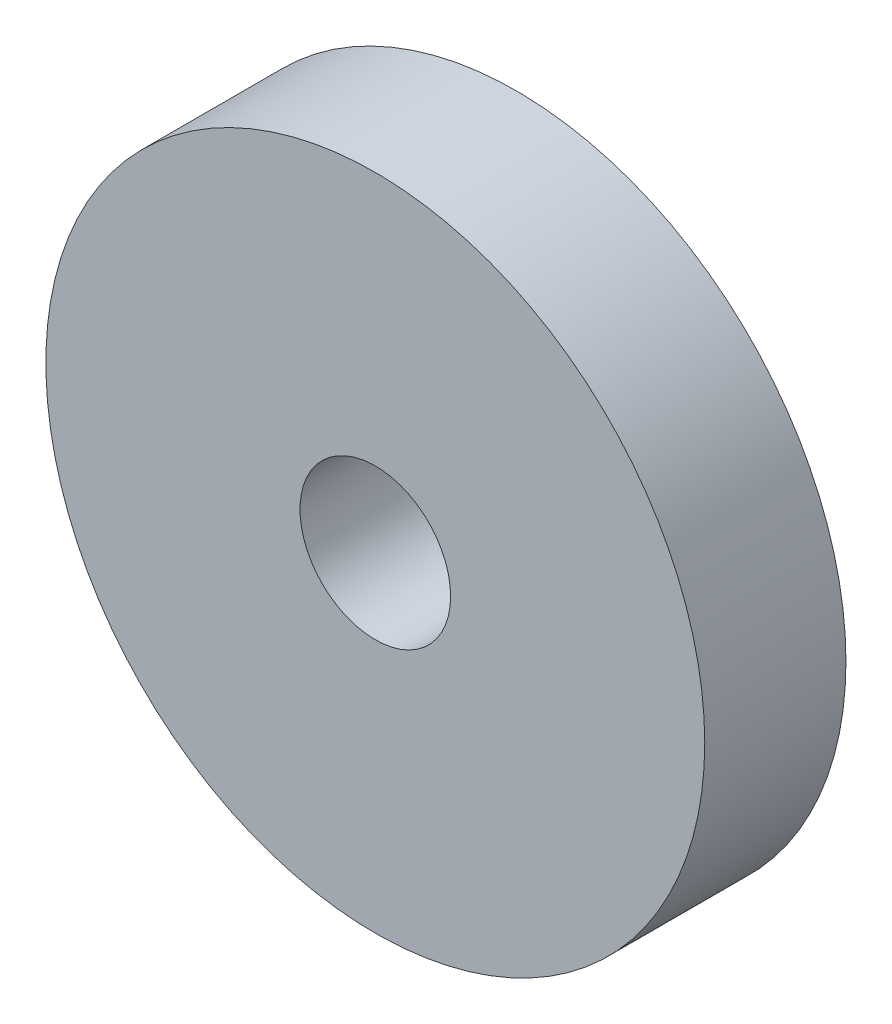
SolidWorks part; units mm, degrees
ref_plane "Front Plane" through (0, 0, 0) normal (0, 0, 1) x (1, 0, 0)
ref_plane "Top Plane" through (0, 0, 0) normal (0, 1, 0) x (1, 0, 0)
ref_plane "Right Plane" through (0, 0, 0) normal (1, 0, 0) x (0, 0, -1)
sketch "Sketch1" plane through (0, 0, 0) normal (0, 0, 1) x (1, 0, 0)
  circle A1 centre (0, 0) radius 7
extrude "Boss-Extrude1" add sketch "Sketch1" along normal blind 3
sketch "Sketch2" plane through (0, 0, 3) normal (0, 0, 1) x (1, 0, 0)
  circle A0 centre (0, 0) radius 1.6
extrude "Cut-Extrude1" cut sketch "Sketch2" against normal up to surface (3 mm away) up to face at (7, 0, 0)
